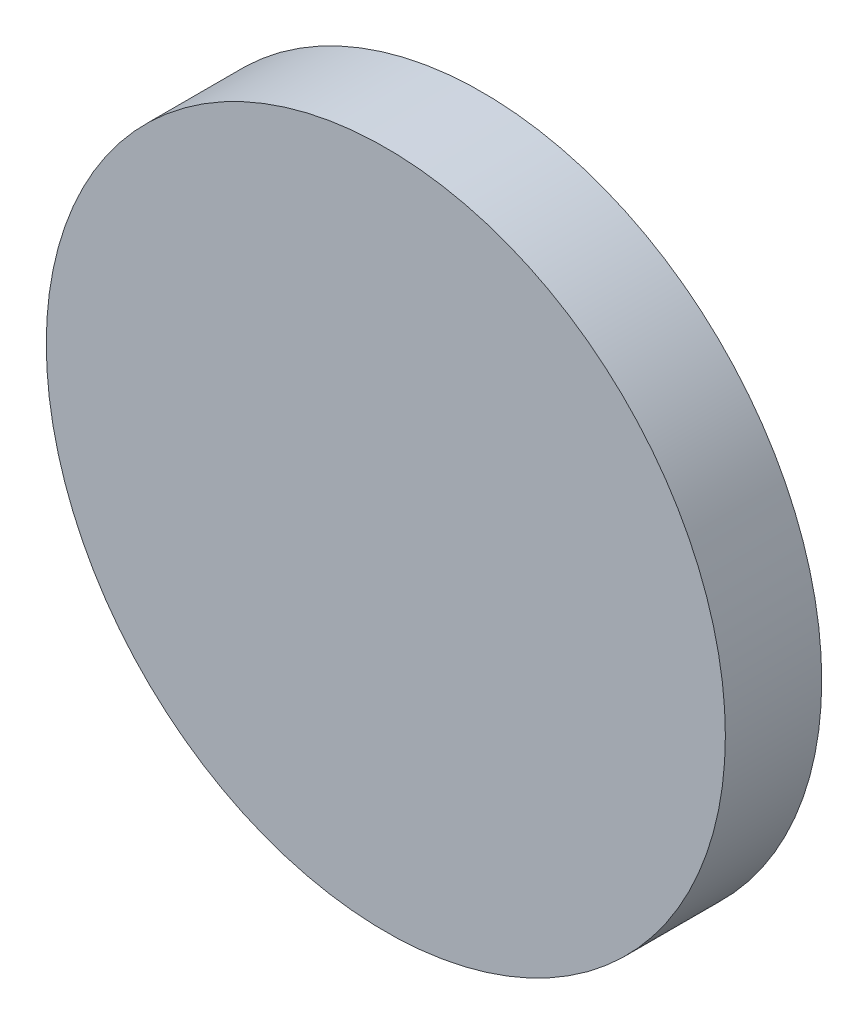
SolidWorks part; units mm, degrees
ref_plane "Front Plane" through (0, 0, 0) normal (0, 0, 1) x (1, 0, 0)
ref_plane "Top Plane" through (0, 0, 0) normal (0, 1, 0) x (1, 0, 0)
ref_plane "Right Plane" through (0, 0, 0) normal (1, 0, 0) x (0, 0, -1)
sketch "Sketch1" plane through (0, 0, 0) normal (1, 0, 0) x (0, 0, -1)
  line L0 (-53.8355, 0) -> (54.6766, 0) construction
  line L1 (-2.597, 0) -> (-2.597, 136.52)
  line L2 (-2.597, 136.52) -> (36.1452, 136.52)
  line L3 (36.1452, 136.52) -> (36.1452, 133.52)
  line L4 (36.1452, 133.52) -> (1.1452, 133.52)
  line L5 (1.1452, 133.52) -> (1.1452, 98)
  line L6 (1.1452, 98) -> (36.1452, 98)
  line L7 (36.1452, 98) -> (36.1452, 95)
  line L8 (36.1452, 95) -> (29.4831, 95)
  line L9 (0.403, 95) -> (0.403, 0)
  line L10 (0.403, 0) -> (-2.597, 0)
  line L11 (25.373, 95) -> (0.403, 95)
  line L13 (29.4831, 95) -> (29.4831, 96.2574)
  line L14 (29.4831, 96.2574) -> (25.373, 96.2574)
  line L15 (25.373, 95) -> (25.373, 96.2574)
  dimension "D1" = 136.52
  dimension "D2" = 3
  dimension "D3" = 3
  dimension "D4" = 95
  dimension "D5" = 3
  dimension "D6" = 35
  dimension "D7" = 35
revolve "Revolve1" add sketch "Sketch1" angle 360 about L0
